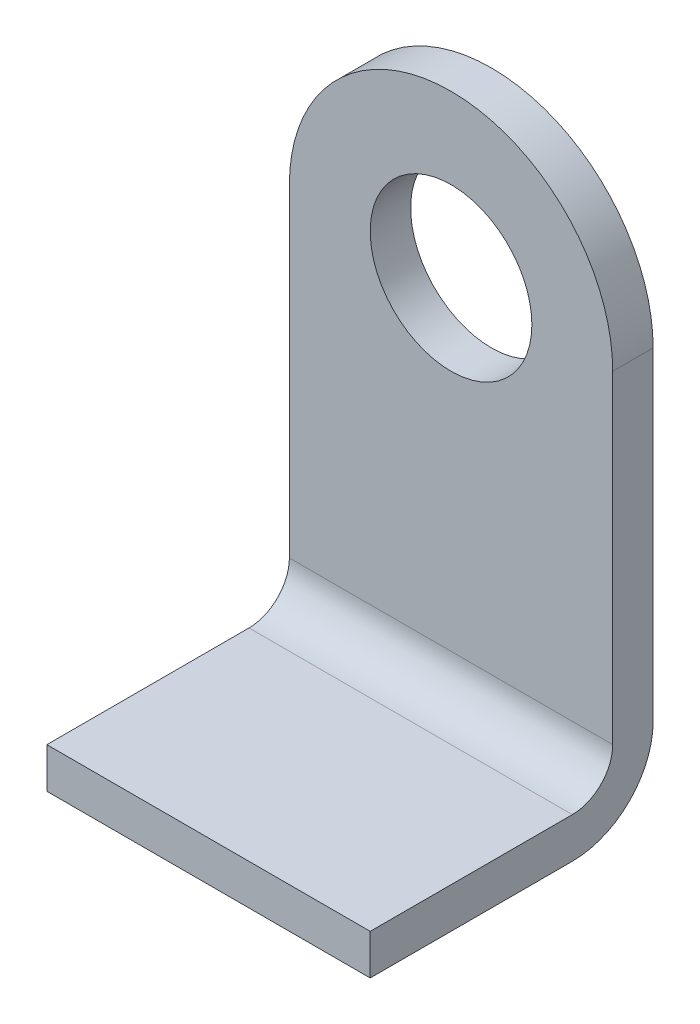
SolidWorks part; units mm, degrees
material "Plain Carbon Steel"
ref_plane "Front Plane" through (0, 0, 0) normal (0, 0, 1) x (1, 0, 0)
ref_plane "Top Plane" through (0, 0, 0) normal (0, 1, 0) x (1, 0, 0)
ref_plane "Right Plane" through (0, 0, 0) normal (1, 0, 0) x (0, 0, -1)
sketch "Sketch1" plane through (0, 0, 0) normal (0, 0, 1) x (1, 0, 0)
  line L0 (0, 40) -> (0, 0)
  line L1 (0, 0) -> (-40, 0)
  line L2 (-40, 0) -> (-40, 40)
  arc A0 (-40, 40) -> (0, 40) centre (-20, 40) cw
  dimension "D1" = 40
  dimension "D2" = 40
extrude "Extrude1" add sketch "Sketch1" along normal blind 5
sketch "Sketch2" plane through (0, 0, 5) normal (0, 0, 1) x (1, 0, 0)
  circle A0 centre (-20, 40) radius 10
  dimension "D1" = 20
extrude "Cut-Extrude1" cut sketch "Sketch2" against normal through all
sketch "Sketch3" plane through (0, 0, 0) normal (1, 0, 0) x (0, 0, -1)
  line L0 (0, 0) -> (0, 40) construction
  line L1 (-5, 0) -> (-5, 40) construction
  line L4 (-10, -5) -> (-35, -5)
  line L5 (-35, -5) -> (-35, -10)
  line L6 (-35, -10) -> (-10, -10)
  line L7 (-5, 0) -> (0, 0) construction
  line L8 (-5, 0) -> (0, 0)
  arc A0 (-5, 0) -> (-10, -5) centre (-10, 0) cw
  arc A1 (0, 0) -> (-10, -10) centre (-10, 0) cw
  dimension "D1" = 5
  dimension "D2" = 5
  dimension "D3" = 25
extrude "Boss-Extrude1" add sketch "Sketch3" against normal up to surface (40 mm away) up to face at (-40, 20, 2.5)
